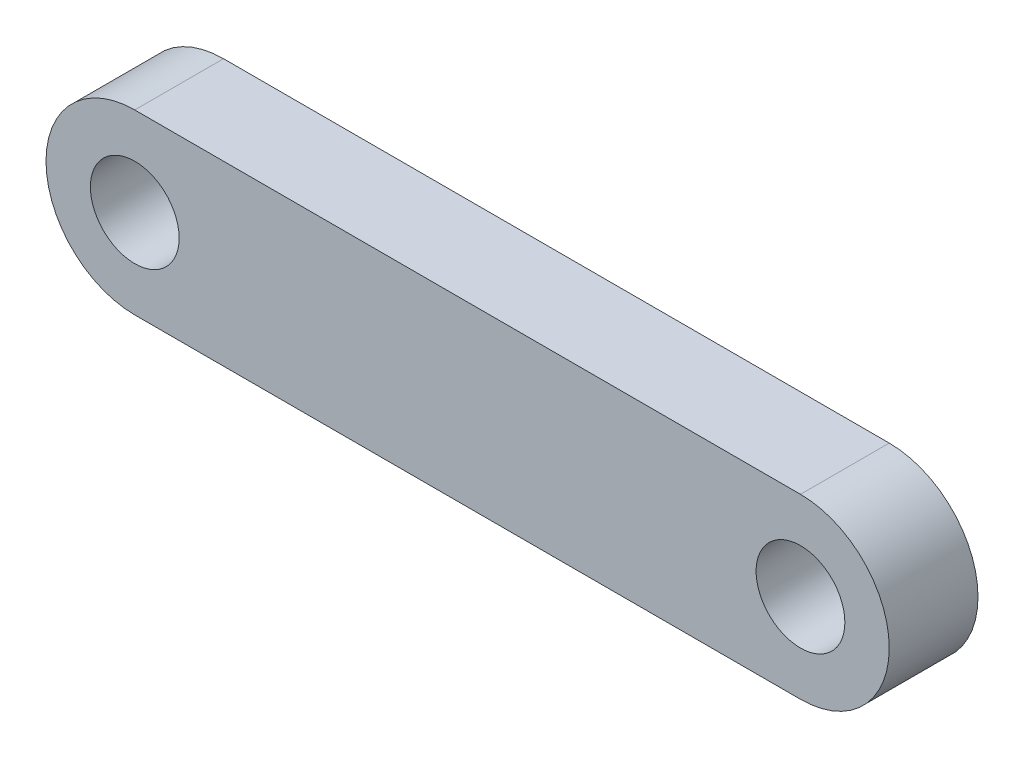
SolidWorks part; units mm, degrees
material "Nylon 101"
ref_plane "Front Plane" through (0, 0, 0) normal (0, 0, 1) x (1, 0, 0)
ref_plane "Top Plane" through (0, 0, 0) normal (0, 1, 0) x (1, 0, 0)
ref_plane "Right Plane" through (0, 0, 0) normal (1, 0, 0) x (0, 0, -1)
sketch "Sketch1" plane through (0, 0, 0) normal (0, 0, 1) x (1, 0, 0)
  line L0 (-37.5, 0) -> (37.5, 0) construction
  line L1 (-37.5, 10) -> (37.5, 10)
  line L2 (-37.5, -10) -> (37.5, -10)
  arc A0 (-37.5, 10) -> (-37.5, -10) centre (-37.5, 0) ccw
  arc A1 (37.5, -10) -> (37.5, 10) centre (37.5, 0) ccw
  circle A2 centre (-37.5, 0) radius 5
  circle A3 centre (37.5, 0) radius 5
  point P2 (0, 0)
  dimension "D3" = 10
  dimension "D4" = 10
  dimension "D1" = 75
  dimension "D2" = 20
extrude "Boss-Extrude1" add sketch "Sketch1" against normal blind 10
